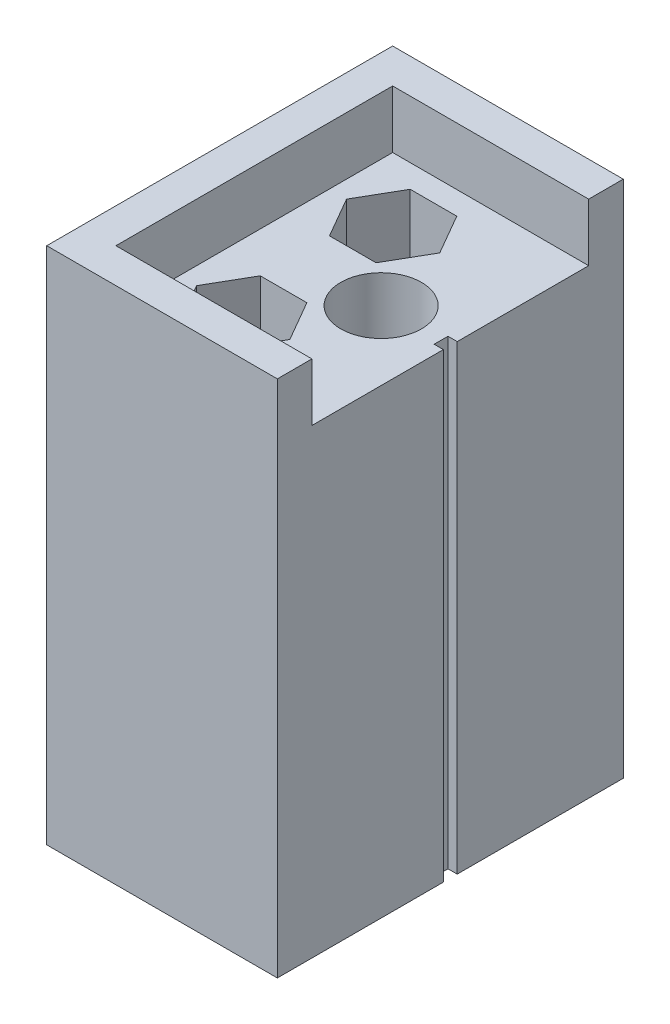
SolidWorks part; units mm, degrees
ref_plane "Front Plane" through (0, 0, 0) normal (0, 0, 1) x (1, 0, 0)
ref_plane "Top Plane" through (0, 0, 0) normal (0, 1, 0) x (1, 0, 0)
ref_plane "Right Plane" through (0, 0, 0) normal (1, 0, 0) x (0, 0, -1)
sketch "Sketch1" plane through (0, 0, 0) normal (0, 1, 0) x (1, 0, 0)
  line L1 (0, 0) -> (20, 0)
  line L2 (0, 0) -> (0, 30)
  line L3 (0, 30) -> (20, 30)
  line L4 (20, 0) -> (20, 30)
  dimension "D1" = 20
  dimension "D2" = 30
extrude "Boss-Extrude1" add sketch "Sketch1" along normal blind 40
sketch "Sketch2" plane through (0, 40, 0) normal (0, 1, 0) x (1, 0, 0)
  line L0 (20, 0) -> (20, 3)
  line L1 (20, 0) -> (20, 30) construction
  line L2 (20, 3) -> (3, 3)
  line L3 (3, 3) -> (3, 27)
  line L4 (3, 27) -> (20, 27)
  line L5 (20, 27) -> (20, 30)
  line L6 (20, 30) -> (0, 30)
  line L7 (0, 30) -> (0, 0)
  line L8 (0, 0) -> (20, 0)
  dimension "D1" = 3
  dimension "D2" = 3
  dimension "D3" = 3
extrude "Boss-Extrude2" add sketch "Sketch2" along normal blind 5
sketch "Sketch3" plane through (0, 40, 0) normal (0, 1, 0) x (1, 0, 0)
  line L0 (3, 3) -> (3, 27) construction
  line L1 (3, 27) -> (20, 27) construction
  line L2 (20, 3) -> (3, 3) construction
  line L3 (3, 27) -> (20, 27) construction
  line L4 (12.5829, 8.5) -> (10.5622, 12)
  line L5 (12.5829, 21.5) -> (10.5622, 25)
  line L6 (10.5622, 25) -> (6.5207, 25)
  line L7 (6.5207, 25) -> (4.5, 21.5)
  line L8 (4.5, 21.5) -> (6.5207, 18)
  line L9 (6.5207, 18) -> (10.5622, 18)
  line L10 (10.5622, 18) -> (12.5829, 21.5)
  line L11 (10.5622, 12) -> (6.5207, 12)
  line L12 (6.5207, 12) -> (4.5, 8.5)
  line L13 (4.5, 8.5) -> (6.5207, 5)
  line L14 (6.5207, 5) -> (10.5622, 5)
  line L15 (10.5622, 5) -> (12.5829, 8.5)
  circle A0 centre (14, 15) radius 3.5
  circle A1 centre (8.5415, 21.5) radius 3.5 construction
  circle A2 centre (8.5415, 8.5) radius 3.5 construction
  dimension "D1" = 7
  dimension "D2" = 11
  dimension "D3" = 12
  dimension "D4" = 7
  dimension "D5" = 2
  dimension "D6" = 1.5
  dimension "D7" = 7
  dimension "D8" = 2
  dimension "D9" = 1.5
extrude "Cut-Extrude1" cut sketch "Sketch3" against normal through all
sketch "Sketch4" plane through (20, 0, 0) normal (1, 0, 0) x (0, 0, -1)
  line L0 (15, 45) -> (15, -0.6619) construction
  line L1 (3, 45) -> (27, 45) construction
  line L2 (15, -0.6619) -> (15, 44.794) construction
  line L3 (3, 40) -> (27, 40) construction
  line L4 (14.4, 40) -> (15.6, 40)
  line L5 (14.4, 40) -> (14.4, 0)
  line L6 (14.4, 0) -> (15.6, 0)
  line L7 (15.6, 40) -> (15.6, 0)
  line L8 (0, 0) -> (30, 0) construction
  dimension "D1" = 1.2
  dimension "D2" = 0.6
extrude "Cut-Extrude2" cut sketch "Sketch4" against normal blind 0.8
